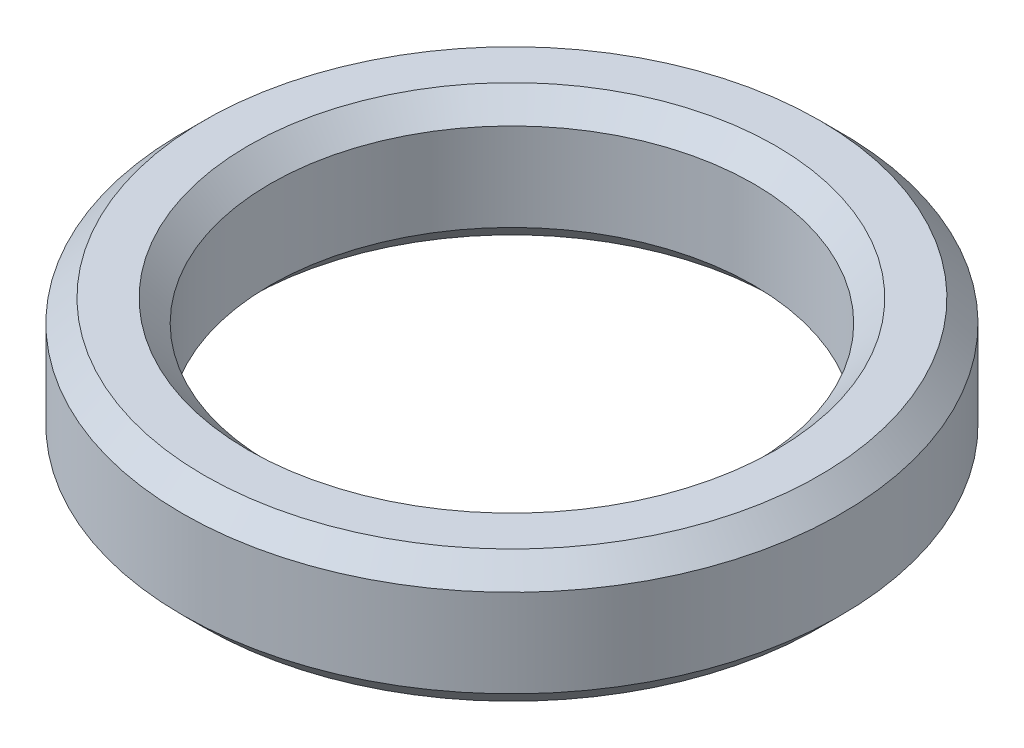
SolidWorks part; units mm, degrees
material "普通碳钢"
ref_plane "前视基准面" through (0, 0, 0) normal (0, 0, 1) x (1, 0, 0)
ref_plane "上视基准面" through (0, 0, 0) normal (0, 1, 0) x (1, 0, 0)
ref_plane "右视基准面" through (0, 0, 0) normal (1, 0, 0) x (0, 0, -1)
sketch "草图1" plane through (0, 0, 0) normal (0, 1, 0) x (1, 0, 0)
  circle A0 centre (0, 0) radius 7.5
  circle A1 centre (0, 0) radius 5.5
  dimension "D1" = 15
  dimension "D2" = 11
extrude "凸台-拉伸1" add sketch "草图1" along normal blind 3
chamfer "倒角1" distance 0.5 angle 45 4 edges at (0, 0, 5.5) (0, 0, 7.5) (0, 3, 5.5) (0, 3, 7.5)
